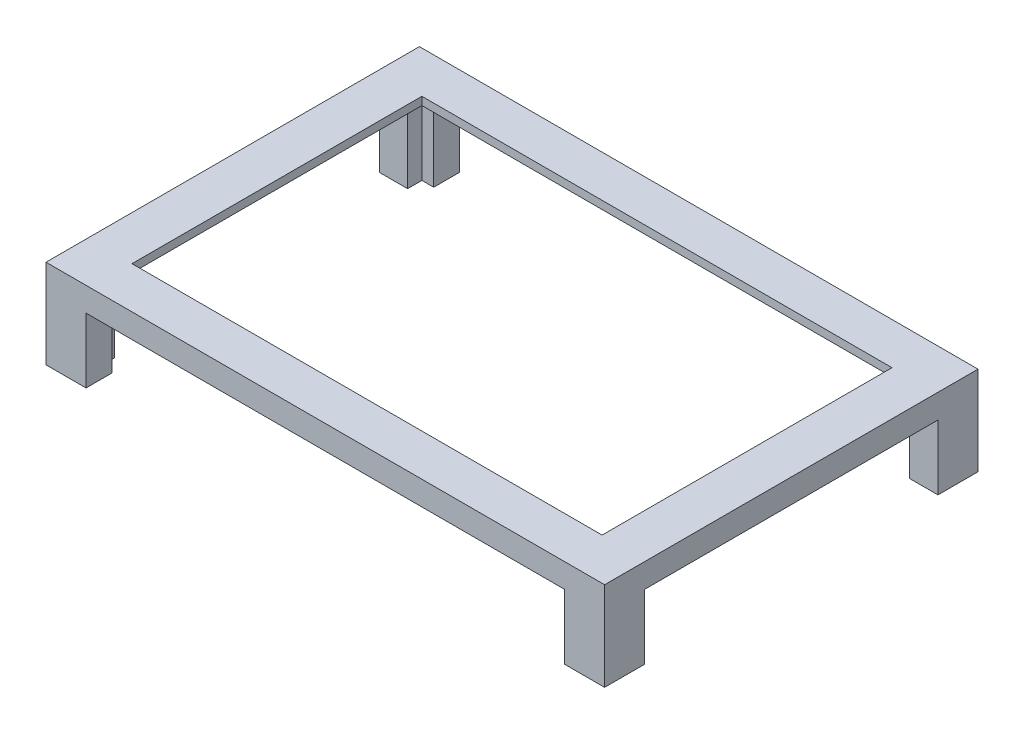
SolidWorks part; units mm, degrees
ref_plane "Front Plane" through (0, 0, 0) normal (0, 0, 1) x (1, 0, 0)
ref_plane "Top Plane" through (0, 0, 0) normal (0, 1, 0) x (1, 0, 0)
ref_plane "Right Plane" through (0, 0, 0) normal (1, 0, 0) x (0, 0, -1)
sketch "Sketch1" plane through (0, 0, 0) normal (0, 1, 0) x (1, 0, 0)
  line L12 (0, 0) -> (-0.254, 0)
  line L13 (-0.254, 0) -> (-0.254, 0.254)
  line L15 (-0.254, 0.254) -> (159.004, 0.254)
  line L16 (-0.254, 0.254) -> (-0.254, -101.854)
  line L17 (-0.254, -101.854) -> (159.004, -101.854)
  line L18 (159.004, 0.254) -> (159.004, -101.854)
  line L20 (167.9575, -110.0137) -> (-9.2075, -110.0137)
  line L21 (167.9575, -110.0137) -> (167.9575, 8.4138)
  line L22 (167.9575, 8.4138) -> (-9.2075, 8.4138)
  line L23 (-9.2075, -110.0137) -> (-9.2075, 8.4138)
  point P8 (79.375, 0)
  point P11 (158.75, -50.8)
  dimension "D1" = 79.375
  dimension "D2" = 158.75
  dimension "D3" = 159.004
  dimension "D4" = 167.9575
  dimension "D5" = 0.254
  dimension "D6" = 9.2075
  dimension "D7" = 8.4138
  dimension "D8" = 50.8
  dimension "D9" = 101.854
  dimension "D10" = 110.0137
extrude "Boss-Extrude1" add sketch "Sketch1" against normal blind 28.194
sketch "Sketch2" plane through (0, 0, -0.254) normal (0, 0, 1) x (1, 0, 0)
  line L0 (159.004, -28.194) -> (159.004, 0) construction
  line L1 (-0.254, 0) -> (159.004, 0)
  line L2 (-0.254, 0) -> (-0.254, -2.54)
  line L3 (-0.254, -2.54) -> (159.004, -2.54)
  line L4 (159.004, 0) -> (159.004, -2.54)
  dimension "D1" = 2.54
extrude "Boss-Extrude2" add sketch "Sketch2" along normal blind 5.08
sketch "Sketch3" plane through (-0.254, 0, 0) normal (1, 0, 0) x (0, 0, -1)
  line L0 (-4.826, 0) -> (-4.826, -2.54) construction
  line L1 (-101.854, 0) -> (-4.826, 0)
  line L2 (-101.854, 0) -> (-101.854, -2.54)
  line L3 (-101.854, -2.54) -> (-4.826, -2.54)
  line L4 (-4.826, 0) -> (-4.826, -2.54)
  dimension "D1" = 2.54
extrude "Boss-Extrude3" add sketch "Sketch3" along normal blind 5.08
sketch "Sketch4" plane through (0, 0, 101.854) normal (0, 0, -1) x (-1, 0, 0)
  line L1 (-159.004, 0) -> (-4.826, 0)
  line L2 (-159.004, 0) -> (-159.004, -2.54)
  line L3 (-159.004, -2.54) -> (-4.826, -2.54)
  line L4 (-4.826, 0) -> (-4.826, -2.54)
extrude "Boss-Extrude4" add sketch "Sketch4" along normal blind 5.08
sketch "Sketch5" plane through (159.004, 0, 0) normal (-1, 0, 0) x (0, 0, 1)
  line L1 (4.826, 0) -> (96.774, 0)
  line L2 (4.826, 0) -> (4.826, -2.54)
  line L3 (4.826, -2.54) -> (96.774, -2.54)
  line L4 (96.774, 0) -> (96.774, -2.54)
  dimension "D1" = 2.54
extrude "Boss-Extrude5" add sketch "Sketch5" along normal blind 5.08
sketch "Sketch9" plane through (0, 0, 110.0137) normal (0, 0, 1) x (1, 0, 0)
  line L0 (167.9575, -28.194) -> (-9.2075, -28.194) construction
  line L1 (3.4925, -7.62) -> (155.2575, -7.62)
  line L2 (3.4925, -7.62) -> (3.4925, -28.194)
  line L3 (3.4925, -28.194) -> (155.2575, -28.194)
  line L4 (155.2575, -7.62) -> (155.2575, -28.194)
  line L5 (167.9575, 0) -> (-9.2075, 0) construction
  line L6 (-9.2075, -28.194) -> (-9.2075, 0) construction
  line L7 (167.9575, -28.194) -> (167.9575, 0) construction
  dimension "D1" = 7.62
  dimension "D2" = 12.7
  dimension "D3" = 12.7
sketch "Sketch10" plane through (-9.2075, 0, 0) normal (-1, 0, 0) x (0, 0, 1)
  line L0 (110.0137, -28.194) -> (-8.4138, -28.194) construction
  line L1 (4.2862, -7.62) -> (97.3137, -7.62)
  line L2 (4.2862, -7.62) -> (4.2862, -28.194)
  line L3 (4.2862, -28.194) -> (97.3137, -28.194)
  line L4 (97.3137, -7.62) -> (97.3137, -28.194)
  line L5 (110.0137, 0) -> (-8.4138, 0) construction
  line L6 (-8.4138, -28.194) -> (-8.4138, 0) construction
  line L7 (110.0137, -7.62) -> (110.0137, -28.194) construction
  dimension "D1" = 7.62
  dimension "D2" = 12.7
  dimension "D3" = 12.7
extrude "Cut-Extrude4" cut sketch "Sketch10" against normal blind 198.628
extrude "Cut-Extrude5" cut sketch "Sketch9" against normal blind 198.628
sketch "Sketch11" plane through (0, -28.194, 0) normal (0, -1, 0) x (1, 0, 0)
  line L0 (-9.2075, 110.0137) -> (-9.2075, 97.3137) construction
  line L2 (167.9575, 110.0137) -> (167.9575, 97.3137) construction
  line L3 (3.4925, 110.0137) -> (-9.2075, 110.0137) construction
  circle A0 centre (-4.8895, 106.5847) radius 1.378
  circle A3 centre (-4.8895, -4.9213) radius 1.378
  circle A5 centre (163.7665, -4.9213) radius 1.378
  circle A6 centre (163.7665, 106.5847) radius 1.378
  dimension "D3" = 2.7559
  dimension "D1" = 2.7559
  dimension "D2" = 2.7559
  dimension "D4" = 2.7559
  dimension "D6" = 4.318
  dimension "D5" = 168.656
  dimension "D7" = 4.191
  dimension "D8" = 111.506
  dimension "D9" = 3.429
extrude "Cut-Extrude6" cut sketch "Sketch11" against normal blind 12.7
